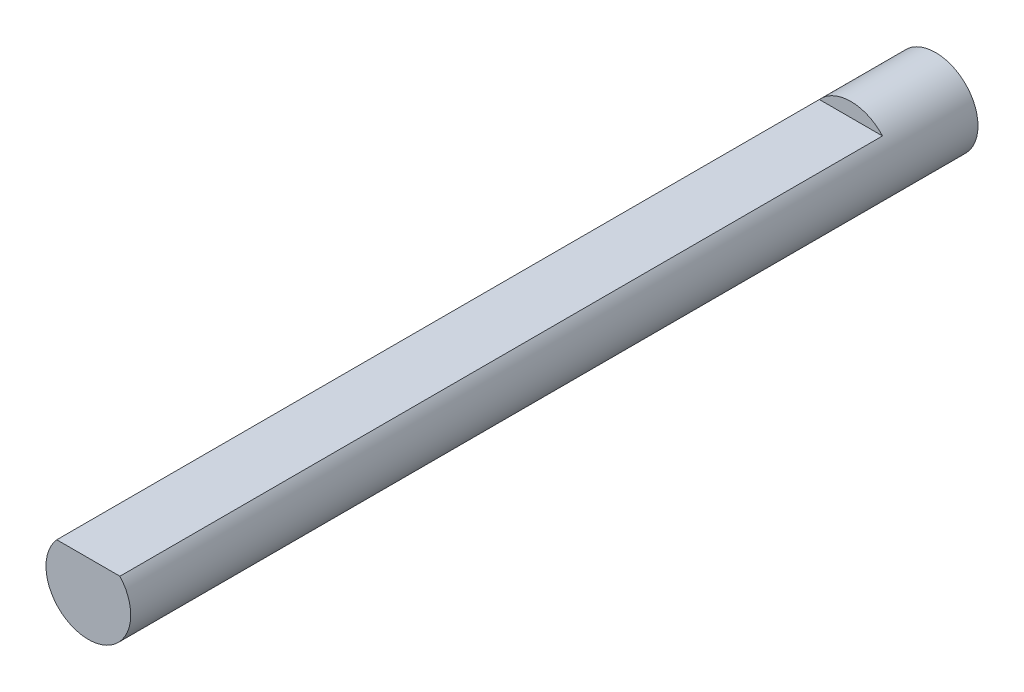
SolidWorks part; units mm, degrees
ref_plane "Front Plane" through (0, 0, 0) normal (0, 0, 1) x (1, 0, 0)
ref_plane "Top Plane" through (0, 0, 0) normal (0, 1, 0) x (1, 0, 0)
ref_plane "Right Plane" through (0, 0, 0) normal (1, 0, 0) x (0, 0, -1)
sketch "Sketch1" plane through (0, 0, 0) normal (0, 0, 1) x (1, 0, 0)
  circle A0 centre (0, 0) radius 1.5
  dimension "D1" = 3
extrude "Boss-Extrude1" add sketch "Sketch1" along normal mid plane 30
sketch "Sketch2" plane through (0, 0, 15) normal (0, 0, 1) x (1, 0, 0)
  line L0 (1.118, 1) -> (-1.118, 1)
  circle A0 centre (0, 0) radius 1.5 construction
  arc A1 (1.118, 1) -> (-1.118, 1) centre (0, 0) ccw
  dimension "D1" = 1
extrude "Cut-Extrude1" cut sketch "Sketch2" against normal blind 27
